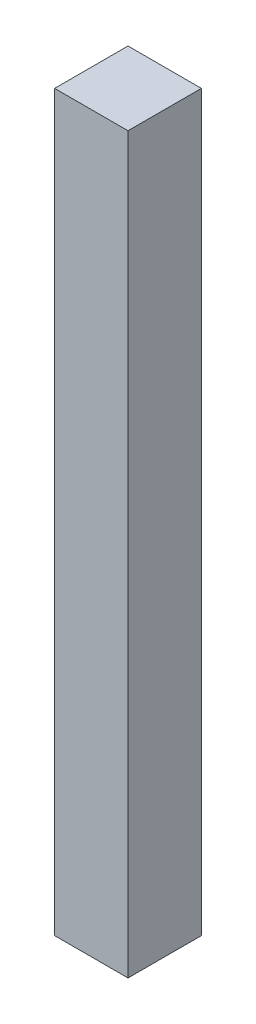
SolidWorks part; units mm, degrees
ref_plane "Спереди" through (0, 0, 0) normal (0, 0, 1) x (1, 0, 0)
ref_plane "Сверху" through (0, 0, 0) normal (0, 1, 0) x (1, 0, 0)
ref_plane "Справа" through (0, 0, 0) normal (1, 0, 0) x (0, 0, -1)
sketch "Эскиз1" plane through (0, 0, 0) normal (0, 1, 0) x (1, 0, 0)
  line L1 (0, 0) -> (120, 0)
  line L2 (0, 0) -> (0, 120)
  line L3 (0, 120) -> (120, 120)
  line L4 (120, 0) -> (120, 120)
extrude "Бобышка-Вытянуть1" add sketch "Эскиз1" along normal blind 1200
